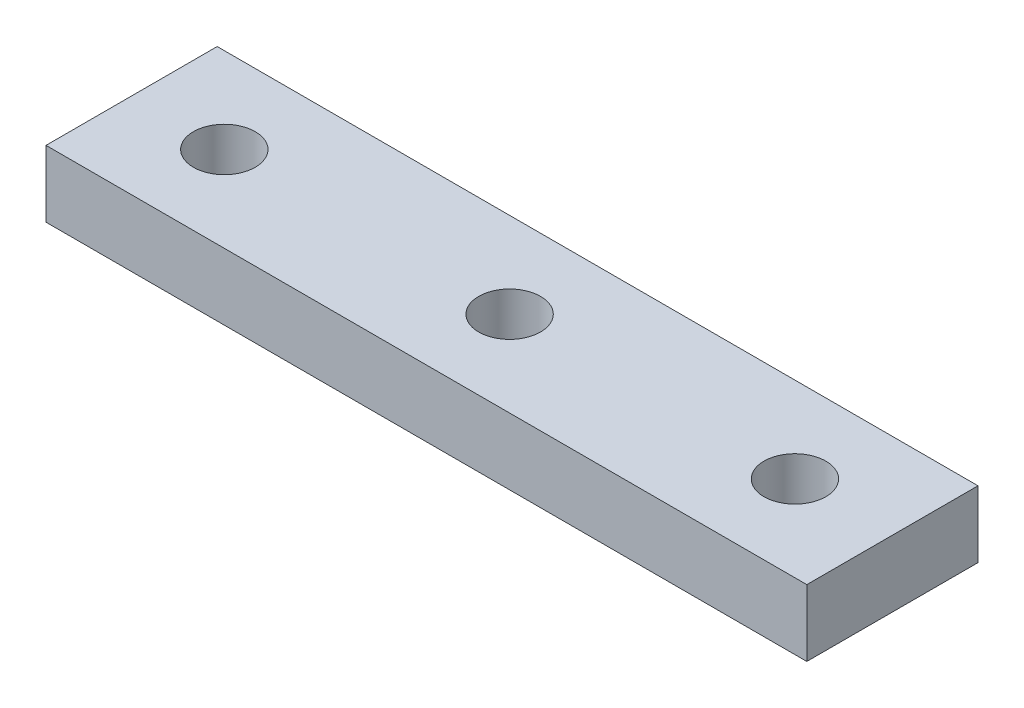
SolidWorks part; units mm, degrees
ref_plane "前视基准面" through (0, 0, 0) normal (0, 0, 1) x (1, 0, 0)
ref_plane "上视基准面" through (0, 0, 0) normal (0, 1, 0) x (1, 0, 0)
ref_plane "右视基准面" through (0, 0, 0) normal (1, 0, 0) x (0, 0, -1)
sketch "草图1" plane through (0, 0, 0) normal (0, 1, 0) x (1, 0, 0)
  line L1 (0, 0) -> (80, 0)
  line L2 (0, 0) -> (0, -18)
  line L3 (0, -18) -> (80, -18)
  line L4 (80, 0) -> (80, -18)
  dimension "D1" = 80
  dimension "D2" = 18
extrude "凸台-拉伸1" add sketch "草图1" along normal blind 7
sketch "草图2" plane through (0, 7, 0) normal (0, 1, 0) x (1, 0, 0)
  line L0 (80, 0) -> (0, 0) construction
  line L1 (0, 0) -> (0, -18) construction
  circle A0 centre (9.75, -9) radius 3.25
  circle A1 centre (39.75, -9) radius 3.25
  circle A2 centre (69.75, -9) radius 3.25
  dimension "D1" = 6.5
  dimension "D2" = 6.5
  dimension "D3" = 6.5
  dimension "D4" = 9
  dimension "D5" = 9
  dimension "D6" = 9
  dimension "D7" = 9.75
  dimension "D8" = 30
  dimension "D9" = 30
extrude "切除-拉伸1" cut sketch "草图2" against normal blind 5
sketch "草图3" plane through (0, 0, 0) normal (0, -1, 0) x (1, 0, 0)
  circle A0 centre (9.75, 9) radius 1.75
  circle A7 centre (39.75, 9) radius 1.75
  circle A8 centre (69.75, 9) radius 1.75
  dimension "D5" = 3.5
  dimension "D6" = 3.5
  dimension "D7" = 3.5
extrude "切除-拉伸3" cut sketch "草图3" against normal through all
